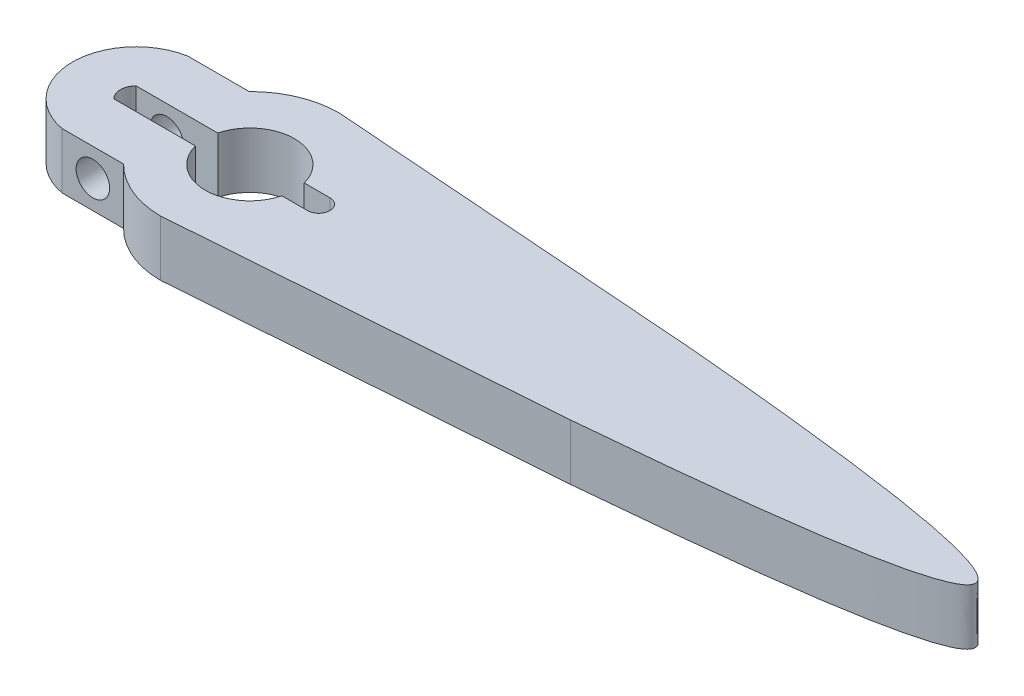
SolidWorks part; units mm, degrees
ref_plane "Front Plane" through (0, 0, 0) normal (0, 0, 1) x (1, 0, 0)
ref_plane "Top Plane" through (0, 0, 0) normal (0, 1, 0) x (1, 0, 0)
ref_plane "Right Plane" through (0, 0, 0) normal (1, 0, 0) x (0, 0, -1)
sketch "Sketch1" plane through (0, 0, 0) normal (0, 1, 0) x (1, 0, 0)
  line L0 (0, 0) -> (-2.5, 0) construction
  line L1 (-2.5, 0) -> (62.5, 0) construction
  line L2 (-2.5, 3.5) -> (-2.5, 8) construction
  line L3 (-2.5, 8) -> (31.6903, 5.4628)
  line L4 (-2.5, -8) -> (31.6903, -5.4628)
  circle A0 centre (-2.5, 0) radius 4
  arc A2 (-2.5, 8) -> (-2.5, -8) centre (-2.5, 0) ccw
  spline S0 degree 2 poles (31.6903, 5.4628) (93.3097, 0) (31.6903, -5.4628) knots 0 0 0 1 1 1
  dimension "D2" = 8
  dimension "D4" = 8
  dimension "D1" = 2.5
  dimension "D3" = 65
extrude "Boss-Extrude1" add sketch "Sketch1" along normal blind 5
sketch "Sketch2" plane through (0, 0, 0) normal (0, -1, 0) x (1, 0, 0)
  circle A0 centre (-2.5, 0) radius 4
  circle A1 centre (-2.5, 0) radius 5
  dimension "D1" = 8
  dimension "D2" = 1
sketch "Sketch5" plane through (0, 5, 0) normal (0, 1, 0) x (1, 0, 0)
  line L0 (3.6723, -1.0007) -> (3.6723, 0) construction
  line L3 (1.3728, -1.0007) -> (3.6723, -1.0007)
  line L4 (4.8948, 0) -> (1.5, 0) construction
  line L5 (1.3728, 1.0007) -> (3.6723, 1.0007)
  line L6 (-6.5, 0) -> (-6.373, 0) construction
  line L7 (-6.373, 0) -> (-6.373, 1) construction
  line L8 (-6.373, 1) -> (-10.4373, 1)
  line L9 (-6.373, -1) -> (-10.4373, -1)
  arc A0 (1.3728, 1.0007) -> (1.3728, -1.0007) centre (-2.5, 0) cw
  circle A3 centre (-2.5, 0) radius 4 construction
  arc A4 (3.6723, -1.0007) -> (3.6723, 1.0007) centre (3.6723, 0) ccw
  arc A5 (-6.373, 1) -> (-6.373, -1) centre (-2.5, 0) ccw
  arc A7 (-2.5, 8) -> (-2.5, -8) centre (-2.5, 0) ccw construction
  arc A8 (-10.4373, 1) -> (-10.4373, -1) centre (-2.5, 0) ccw
  dimension "D2" = 1
extrude "Cut-Extrude1" cut sketch "Sketch5" against normal through all
sketch "Sketch6" plane through (0, 5, 0) normal (0, 1, 0) x (1, 0, 0)
  line L0 (-10.4373, 1) -> (-13.6873, 1)
  line L1 (-2.5004, 4) -> (-2.5, 0) construction
  line L2 (-8.1873, 5.6263) -> (-13.6873, 5.6263)
  line L3 (-13.6873, 5.6263) -> (-13.6873, 1) construction
  line L4 (-2.5, 0) -> (-12.6782, 0) construction
  line L5 (-8.1873, -5.6263) -> (-13.6873, -5.6263)
  line L6 (-10.4373, -1) -> (-13.6873, -1)
  arc A0 (1.3728, 1.0007) -> (-6.373, 1) centre (-2.5, 0) ccw construction
  arc A1 (-10.4373, 1) -> (-8.1873, 5.6263) centre (-2.5, 0) ccw
  arc A2 (-13.6873, 5.6263) -> (-13.6873, -5.6263) centre (-12.6782, 0) ccw
  arc A3 (-13.6873, 1) -> (-13.6873, -1) centre (-12.6782, 0) ccw
  arc M7 (-10.4373, -1) -> (-2.5, -8) centre (-2.5, 0) ccw
  arc M11 (-2.5, 8) -> (-10.4373, 1) centre (-2.5, 0) ccw
  dimension "D1" = 3.25
  dimension "D2" = 5.5
extrude "Boss-Extrude3" add sketch "Sketch6" against normal blind 5 contours A3 L0 L2 A2 L5 L6 M11 M7
sketch "Sketch7" plane through (0, 0, -5.6263) normal (0, 0, -1) x (-1, 0, 0)
  line L0 (8.1873, 5) -> (10.9373, 5) construction
  line L1 (8.1873, 5) -> (13.6873, 5) construction
  line L2 (10.9373, 5) -> (10.9373, 0) construction
  line L3 (8.1873, 0) -> (13.6873, 0) construction
  line L4 (13.6873, 0) -> (10.9373, 0) construction
  line L5 (10.9373, 0) -> (10.9373, 2.5) construction
  circle A0 centre (10.9373, 2.5) radius 1.5
  dimension "D1" = 3
extrude "Cut-Extrude2" cut sketch "Sketch7" against normal through all both and the other way through all
